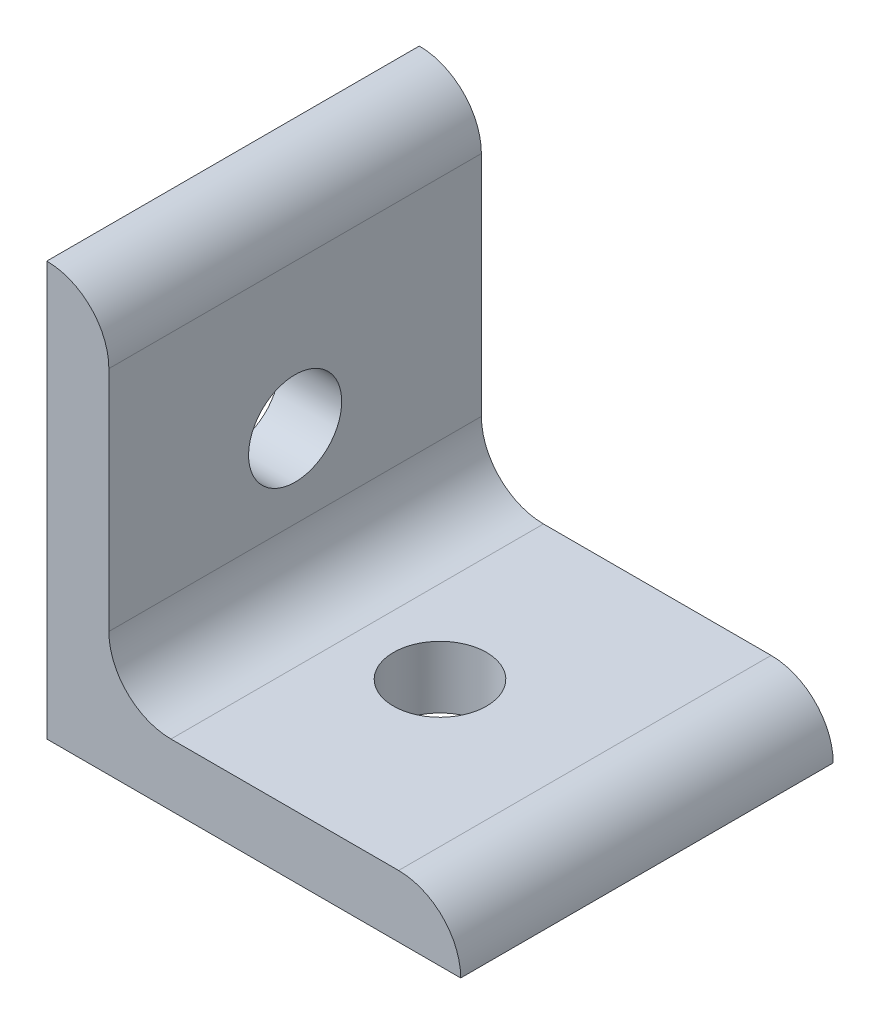
SolidWorks part; units mm, degrees
ref_plane "Front Plane" through (0, 0, 0) normal (0, 0, 1) x (1, 0, 0)
ref_plane "Top Plane" through (0, 0, 0) normal (0, 1, 0) x (1, 0, 0)
ref_plane "Right Plane" through (0, 0, 0) normal (1, 0, 0) x (0, 0, -1)
sketch "Sketch1" plane through (0, 0, 0) normal (0, 0, 1) x (1, 0, 0)
  line L0 (0, 0) -> (0, 40)
  line L1 (6, 34) -> (6, 40) construction
  line L2 (6, 34) -> (6, 12)
  line L3 (12, 6) -> (34, 6)
  line L4 (6, 40) -> (0, 40) construction
  line L5 (40, 0) -> (0, 0)
  line L6 (34, 6) -> (40, 6) construction
  line L7 (40, 6) -> (40, 0) construction
  arc A0 (6, 34) -> (0, 40) centre (0, 34) ccw
  arc A1 (40, 0) -> (34, 6) centre (34, 0) ccw
  arc A2 (6, 12) -> (12, 6) centre (12, 12) ccw
  point P10 (6, 37)
  dimension "E" = 6
  dimension "D" = 6
  dimension "C" = 40
  dimension "B" = 40
extrude "Boss-Extrude1" add sketch "Sketch1" along normal mid plane 36
sketch "Sketch2" plane through (0, 0, 0) normal (0, 1, 0) x (1, 0, 0)
  line L0 (0, 0) -> (20, 0) construction
  circle A0 centre (20, 0) radius 4.5
  dimension "D1" = 20
  dimension "E" = 9
extrude "Cut-Extrude1" cut sketch "Sketch2" along normal through all
sketch "Sketch3" plane through (0, 0, 0) normal (1, 0, 0) x (0, 0, -1)
  line L0 (0, 0) -> (0, 20) construction
  circle A0 centre (0, 20) radius 4.5
  dimension "D1" = 20
  dimension "E" = 9
extrude "Cut-Extrude2" cut sketch "Sketch3" along normal through all
equation "\"E@Sketch3\" = \"E@Sketch2\""
equation "\"D1@Sketch3\" = \"D1@Sketch2\""
